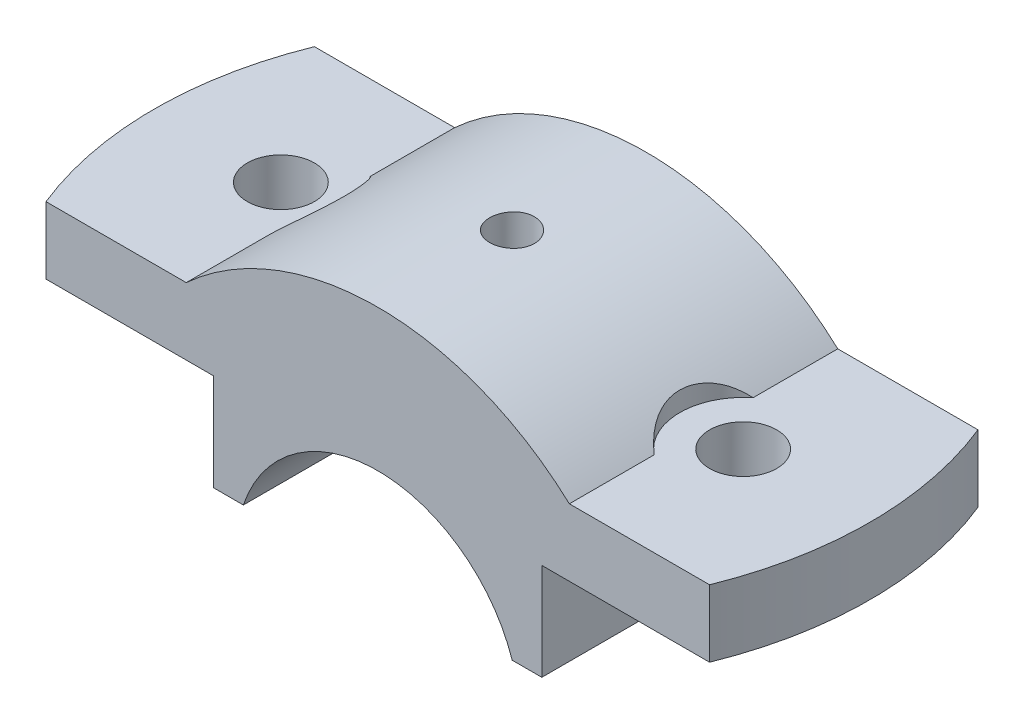
SolidWorks part; units mm, degrees
ref_plane "Front Plane" through (0, 0, 0) normal (0, 0, 1) x (1, 0, 0)
ref_plane "Top Plane" through (0, 0, 0) normal (0, 1, 0) x (1, 0, 0)
ref_plane "Right Plane" through (0, 0, 0) normal (1, 0, 0) x (0, 0, -1)
sketch "Sketch1" plane through (0, 0, 0) normal (0, 0, 1) x (1, 0, 0)
  line L1 (0, 63.7788) -> (0, -45.5865) construction
  line L2 (22, 6) -> (22, 19)
  line L3 (22, 6) -> (18.0278, 6)
  line L4 (22, 19) -> (50, 19)
  line L5 (50, 19) -> (50, 28)
  line L6 (50, 28) -> (25.6905, 28)
  line L7 (-50, 28) -> (-25.6905, 28)
  line L8 (-50, 19) -> (-50, 28)
  line L9 (-22, 6) -> (-22, 19)
  line L10 (-22, 19) -> (-50, 19)
  line L11 (-22, 6) -> (-18.0278, 6)
  arc A0 (18.0278, 6) -> (-18.0278, 6) centre (0, 0) ccw
  arc A1 (25.6905, 28) -> (-25.6905, 28) centre (0, 0) ccw
  dimension "D1" = 50
  dimension "D2" = 19
  dimension "D3" = 38
  dimension "D4" = 9
  dimension "D5" = 13
  dimension "D6" = 6
  dimension "D7" = 44
  dimension "D8" = 19
extrude "Boss-Extrude1" add sketch "Sketch1" along normal mid plane 36
sketch "Sketch4" plane through (0, 28, 0) normal (0, 1, 0) x (1, 0, 0)
  line L0 (-25.6905, 18) -> (-50, 18) construction
  line L1 (-50, -18) -> (-50, 18) construction
  line L2 (-25.6905, -18) -> (-50, -18) construction
  line L3 (50, -18) -> (25.6905, -18) construction
  line L4 (50, -18) -> (50, 18) construction
  line L5 (50, 18) -> (25.6905, 18) construction
  line L6 (-44.4972, 18) -> (-50, 18)
  line L7 (-50, -18) -> (-50, 18)
  line L8 (-44.4972, -18) -> (-50, -18)
  line L9 (50, -18) -> (44.4972, -18)
  line L10 (50, -18) -> (50, 18)
  line L11 (50, 18) -> (44.4972, 18)
  arc A0 (-44.4972, 18) -> (-44.4972, -18) centre (0, 0) ccw
  arc A1 (44.4972, -18) -> (44.4972, 18) centre (0, 0) ccw
  dimension "D1" = 48
extrude "Cut-Extrude1" cut sketch "Sketch4" against normal through all
sketch "Sketch5" plane through (0, 28, 0) normal (0, 1, 0) x (1, 0, 0)
  line L0 (-25.6905, -18) -> (25.6905, -18) construction
  circle A0 centre (-31, 0) radius 4.5
  point P2 (0, -18)
  dimension "D1" = 31
extrude "Cut-Extrude2" cut sketch "Sketch5" against normal through all
mirror "Mirror1" about plane through (0, 0, 0) normal (1, 0, 0) of "Cut-Extrude2"
sketch "Sketch7" plane through (0, 28, 0) normal (0, 1, 0) x (1, 0, 0)
  circle A0 centre (-31, 0) radius 8.5
  dimension "D1" = 17
extrude "Cut-Extrude4" cut sketch "Sketch7" along normal blind 13
hole_wizard "CBORE for M5 Hex Head Bolt1" positions "3DSketch1" profile "Sketch9" counterbore size "M5" standard "ANSI Metric" end condition through all
sketch3d "3DSketch1"
  point P0 (0, 38, 0)
  dimension "D1" = 0
  dimension "D2" = 0
sketch "Sketch9" plane through (0, 38, 0) normal (1, 0, 0) x (0, 0, 1)
  line L0 (0, 0) -> (0, 32)
  line L1 (0, 32) -> (2.5, 32)
  line L3 (2.5, 32) -> (2.5, 13)
  line L4 (2.5, 13) -> (3, 13)
  line L5 (3, 13) -> (3, 0)
  line L7 (3, 0) -> (0, 0)
  line L11 (0, -6.35) -> (0, 107.95) construction
  dimension "Thru Hole Dia." = 5
  dimension "Thru Hole Depth" = 32
  dimension "C'Bore Dia." = 6
  dimension "C'Bore Depth" = 13
mirror "Mirror2" about plane through (0, 0, 0) normal (1, 0, 0) of "Cut-Extrude4"
sketch "Sketch10" plane through (0, 28, 0) normal (0, 1, 0) x (1, 0, 0)
  point P1 (-31, 0)
  point P2 (31, 0)
  dimension "D1" = 62
